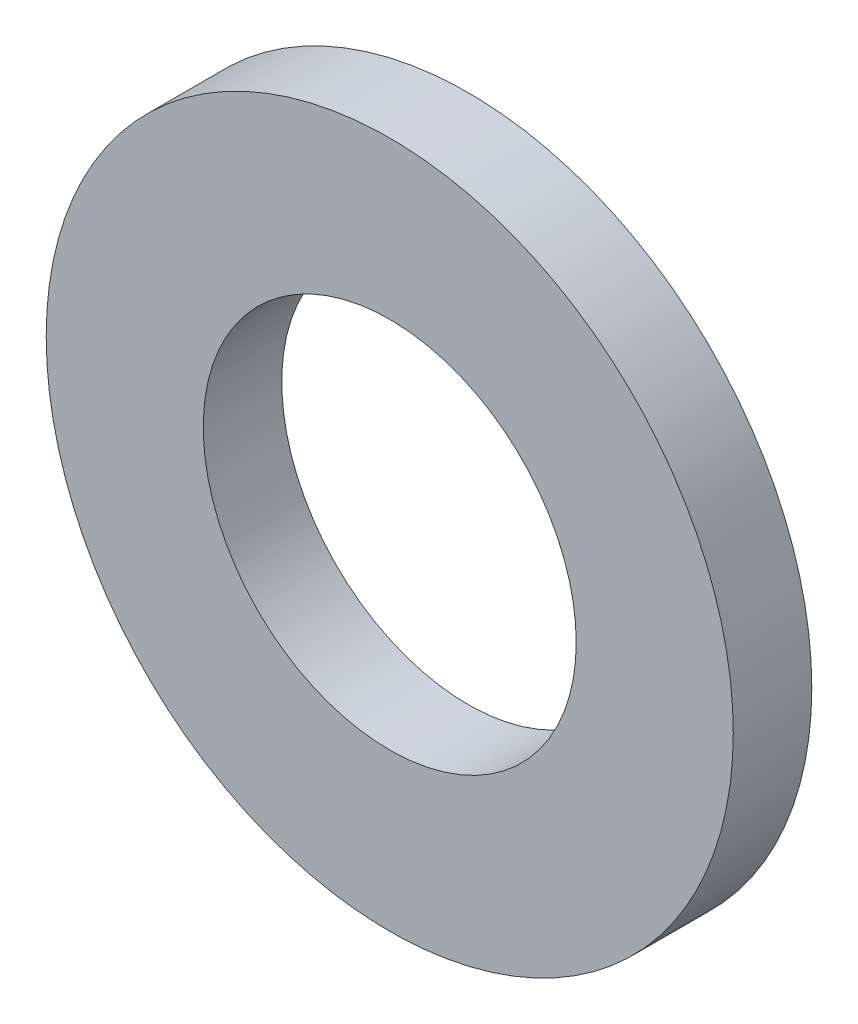
SolidWorks part; units mm, degrees
material "Laiton"
ref_plane "Plan de face" through (0, 0, 0) normal (0, 0, 1) x (1, 0, 0)
ref_plane "Plan de dessus" through (0, 0, 0) normal (0, 1, 0) x (1, 0, 0)
ref_plane "Plan de droite" through (0, 0, 0) normal (1, 0, 0) x (0, 0, -1)
sketch "Esquisse1" plane through (0, 0, 0) normal (0, 0, 1) x (1, 0, 0)
  circle A0 centre (0, 0) radius 1.9
  circle A1 centre (0, 0) radius 3.5
  dimension "D1" = 7
  dimension "D2" = 3.8
extrude "Extrusion1" add sketch "Esquisse1" along normal blind 0.8
